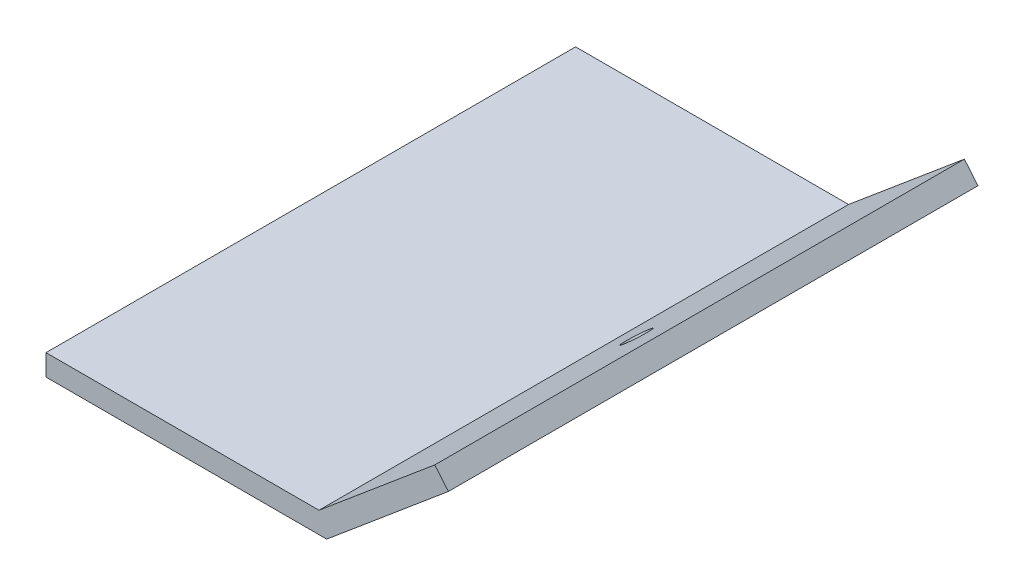
SolidWorks part; units mm, degrees
ref_plane "正面" through (0, 0, 0) normal (0, 0, 1) x (1, 0, 0)
ref_plane "平面" through (0, 0, 0) normal (0, 1, 0) x (1, 0, 0)
ref_plane "右側面" through (0, 0, 0) normal (1, 0, 0) x (0, 0, -1)
sketch "ｽｹｯﾁ1" plane through (0, 0, 0) normal (0, 0, 1) x (1, 0, 0)
  line L0 (0, 0) -> (25.7721, 0)
  line L1 (25.7721, 0) -> (36.7051, 9.1739)
  line L2 (36.7051, 9.1739) -> (37.9907, 7.6418)
  line L3 (37.9907, 7.6418) -> (26.5, -2)
  line L4 (26.5, -2) -> (0, -2)
  line L5 (0, -2) -> (0, 0)
  dimension "D1" = 2
  dimension "D2" = 2
  dimension "D3" = 26.5
  dimension "D4" = 140
  dimension "D6" = 15
extrude "ﾎﾞｽ - 押し出し1" add sketch "ｽｹｯﾁ1" along normal blind 50
sketch "ｽｹｯﾁ2" plane through (10.6484, -12.6903, 0) normal (-0.6428, 0.766, 0) x (0, 0, 1)
  line L0 (25, 19.7425) -> (25, 26.2425)
  line L1 (50, 19.7425) -> (0, 19.7425) construction
  circle A0 centre (25, 26.2425) radius 1.6
  dimension "D2" = 3.2
  dimension "D1" = 6.5
hole_wizard "M3x0.5 ねじ穴1" positions "3Dｽｹｯﾁ1" profile "ｽｹｯﾁ3" tap size "M3x0.5" standard "JIS"
sketch3d "3Dｽｹｯﾁ1"
  point P0 (30.7513, 4.1781, 25)
sketch "ｽｹｯﾁ3" plane through (30.7513, 4.1781, 25) normal (0, 0, 1) x (-0.766, -0.6428, 0)
  line L0 (0, 0) -> (0, 9.2511)
  line L1 (0, 9.2511) -> (1.25, 8.5)
  line L2 (1.25, 8.5) -> (1.25, 0)
  line L5 (1.25, 0) -> (0, 0)
  line L10 (0, 9.2511) -> (-1.25, 8.5) construction
  line L11 (0, -6.35) -> (0, 107.95) construction
  dimension "ねじ下穴ﾄﾞﾘﾙ直径" = 2.5
  dimension "ねじ下穴ﾄﾞﾘﾙの深さ" = 8.5
  dimension "ﾄﾞﾘﾙ角度" = 118
cosmetic thread "穴のねじ山1" parameters "D1"=2.1076, "D2"=3
